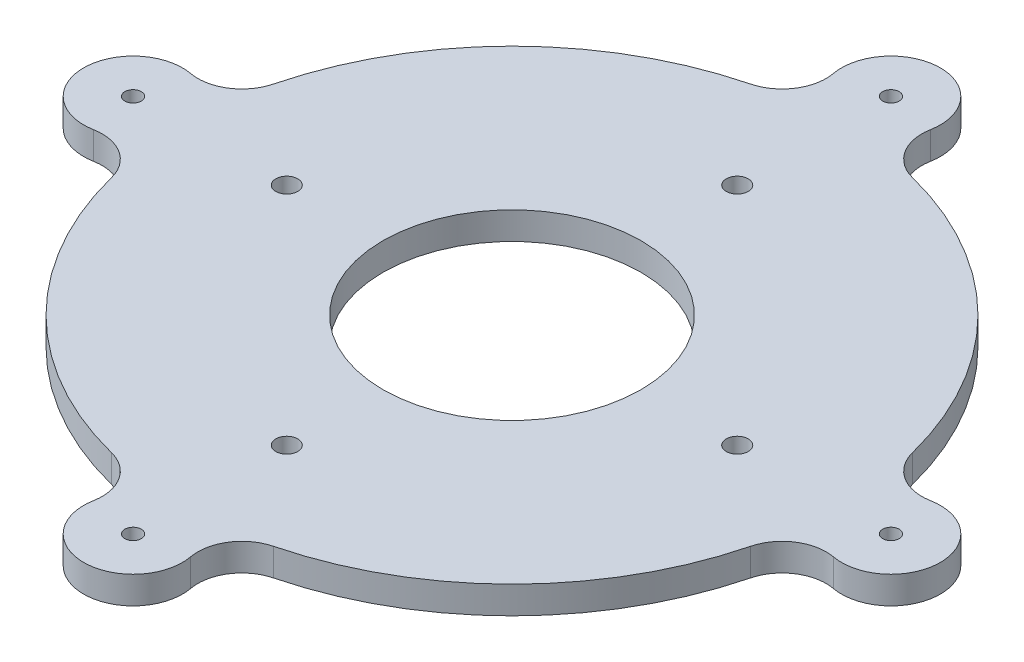
SolidWorks part; units mm, degrees
ref_plane "Front Plane" through (0, 0, 0) normal (0, 0, 1) x (1, 0, 0)
ref_plane "Top Plane" through (0, 0, 0) normal (0, 1, 0) x (1, 0, 0)
ref_plane "Right Plane" through (0, 0, 0) normal (1, 0, 0) x (0, 0, -1)
sketch "Sketch1" plane through (0, 0, 0) normal (0, 1, 0) x (1, 0, 0)
  circle A21 centre (0, 0) radius 23.5
  arc A23 (58.1586, 14.7506) -> (14.7506, 58.1586) centre (0, 0) ccw
  arc A24 (67.3657, -8.8504) -> (67.3657, 8.8504) centre (69, 0) ccw
  arc A25 (58.1586, 14.7506) -> (67.3657, 8.8504) centre (65.913, 16.7174) ccw
  arc A26 (67.3657, -8.8504) -> (58.1586, -14.7506) centre (65.913, -16.7174) ccw
  circle A27 centre (69, 0) radius 1.5
  arc A29 (-67.3657, 8.8504) -> (-67.3657, -8.8504) centre (-69, 0) ccw
  arc A30 (-67.3657, 8.8504) -> (-58.1586, 14.7506) centre (-65.913, 16.7174) ccw
  arc A31 (-58.1586, -14.7506) -> (-67.3657, -8.8504) centre (-65.913, -16.7174) ccw
  arc A32 (8.8504, 67.3657) -> (-8.8504, 67.3657) centre (0, 69) ccw
  arc A33 (8.8504, 67.3657) -> (14.7506, 58.1586) centre (16.7174, 65.913) ccw
  arc A34 (-14.7506, 58.1586) -> (-8.8504, 67.3657) centre (-16.7174, 65.913) ccw
  arc A35 (-8.8504, -67.3657) -> (8.8504, -67.3657) centre (0, -69) ccw
  arc A36 (-8.8504, -67.3657) -> (-14.7506, -58.1586) centre (-16.7174, -65.913) ccw
  arc A37 (14.7506, -58.1586) -> (8.8504, -67.3657) centre (16.7174, -65.913) ccw
  circle A38 centre (0, 0) radius 41.0122 construction
  circle A39 centre (41.0122, 0) radius 2
  circle A41 centre (0, 41.0122) radius 2
  circle A42 centre (-41.0122, 0) radius 2
  circle A43 centre (0, -41.0122) radius 2
  arc A44 (-58.1586, -14.7506) -> (-14.7506, -58.1586) centre (0, 0) ccw
  arc A45 (14.7506, -58.1586) -> (58.1586, -14.7506) centre (0, 0) ccw
  arc A46 (-14.7506, 58.1586) -> (-58.1586, 14.7506) centre (0, 0) ccw
  circle A47 centre (0, 69) radius 1.5
  circle A48 centre (0, -69) radius 1.5
  circle A49 centre (-69, 0) radius 1.5
  dimension "D1" = 47
  dimension "D2" = 120
  dimension "D3" = 18
  dimension "D4" = 16
  dimension "D5" = 16
  dimension "D6" = 3
  dimension "D7" = 18
  dimension "D8" = 65.913
  dimension "D9" = 16
  dimension "D10" = 16
  dimension "D11" = 18
  dimension "D12" = 16
  dimension "D13" = 16
  dimension "D14" = 18
  dimension "D15" = 16
  dimension "D16" = 16
  dimension "D21" = 4
  dimension "D24" = 3
  dimension "D20" = 4
  dimension "D25" = 65.913
  dimension "D17" = 82.0244
  dimension "D18" = 4
  dimension "D19" = 3
  dimension "D22" = 4
  dimension "D23" = 3
  dimension "D26" = 65.913
  dimension "D27" = 65.913
  dimension "D28" = 58
extrude "Boss-Extrude1" add sketch "Sketch1" along normal blind 5
